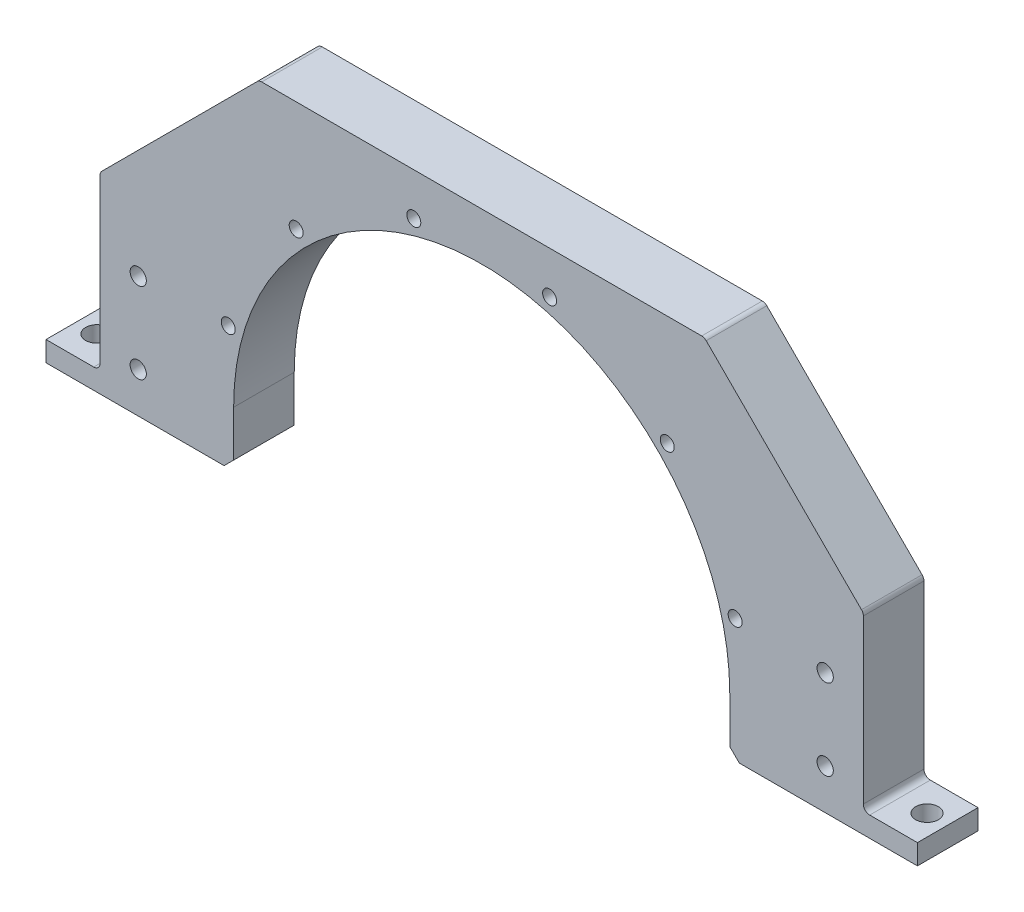
SolidWorks part; units mm, degrees
material "6061-T6 (SS)"
ref_plane "Front Plane" through (0, 0, 0) normal (0, 0, 1) x (1, 0, 0)
ref_plane "Top Plane" through (0, 0, 0) normal (0, 1, 0) x (1, 0, 0)
ref_plane "Right Plane" through (0, 0, 0) normal (1, 0, 0) x (0, 0, -1)
sketch "Sketch1" plane through (0, 0, 0) normal (0, 0, 1) x (1, 0, 0)
  line L1 (78, 0) -> (78, -17.4)
  line L2 (78, -17.4) -> (137, -17.4)
  line L3 (137, -17.4) -> (137, -11.05)
  line L4 (137, -11.05) -> (120, -11.05)
  line L5 (120, -11.05) -> (120, 93)
  line L6 (120, 93) -> (0, 93)
  line L11 (0, 93) -> (0, 78)
  arc A0 (0, 78) -> (78, 0) centre (0, 0) cw
  dimension "D1" = 78
  dimension "D2" = 120
  dimension "D3" = 6.35
  dimension "D4" = 17
  dimension "D5" = 15
  dimension "D6" = 17.4
extrude "Boss-Extrude1" add sketch "Sketch1" along normal blind 19.05
hole_wizard "Tapped Hole for #8-32 Helicoil1" positions "Sketch3" profile "Sketch2" tap size "#8-32" standard "Helicoil® Inch" end condition through all
sketch "Sketch3" plane through (0, 0, 19.05) normal (0, 0, 1) x (1, 0, 0)
  line L0 (0, 0) -> (21.3526, 79.6889)
  line L2 (0, 0) -> (58.3363, 58.3363)
  line L4 (0, 0) -> (79.6889, 21.3526)
  line L6 (21.3526, 79.6889) -> (39.8444, 69.0126)
  line L7 (39.8444, 69.0126) -> (58.3363, 58.3363)
  line L9 (58.3363, 58.3363) -> (69.0126, 39.8444)
  line L10 (69.0126, 39.8444) -> (79.6889, 21.3526)
  line L12 (21.3526, 79.6889) -> (0, 79.6889)
  line L13 (0, 93) -> (0, 78) construction
  line L15 (78, 0) -> (120, 0)
  line L16 (120, -11.05) -> (120, 93) construction
  line L18 (79.6889, 21.3526) -> (79.6889, 0)
  point P0 (21.3526, 79.6889)
  point P2 (58.3363, 58.3363)
  point P4 (79.6889, 21.3526)
  dimension "D1" = 82.5
sketch "Sketch2" plane through (21.3526, 79.6889, 19.05) normal (1, 0, 0) x (0, -1, 0)
  line L0 (0, 0) -> (0, 19.05)
  line L1 (0, 19.05) -> (2.1971, 19.05)
  line L2 (2.1971, 19.05) -> (2.1971, 0)
  line L5 (2.1971, 0) -> (0, 0)
  line L11 (0, -6.35) -> (0, 107.95) construction
  dimension "Thru Tap Drill Dia." = 4.3942
  dimension "Thru Tap Drill Depth" = 19.05
cosmetic thread "Hole Thread1" parameters "D1"=12.7, "D2"=5.2756
cosmetic thread "Hole Thread2" parameters "D1"=12.7, "D2"=5.2756
cosmetic thread "Hole Thread3" parameters "D1"=12.7, "D2"=5.2756
hole_wizard "1/4-20 Tapped Hole1" positions "Sketch7" profile "Sketch8" tap size "1/4-20" standard "ANSI Inch" end condition through all
sketch "Sketch7" plane through (0, 0, 19.05) normal (0, 0, 1) x (1, 0, 0)
  line L0 (108, 20.7) -> (108, -4.7)
  line L2 (78, -17.4) -> (137, -17.4) construction
  point P0 (108, 20.7)
  point P2 (108, -4.7)
  dimension "D1" = 108
  dimension "D2" = 25.4
  dimension "D3" = 12.7
sketch "Sketch8" plane through (108, 20.7, 19.05) normal (1, 0, 0) x (0, -1, 0)
  line L0 (0, 0) -> (0, 19.05)
  line L1 (0, 19.05) -> (2.5527, 19.05)
  line L2 (2.5527, 19.05) -> (2.5527, 0)
  line L5 (2.5527, 0) -> (0, 0)
  line L11 (0, -6.35) -> (0, 107.95) construction
  dimension "Thru Tap Drill Dia." = 5.1054
  dimension "Thru Tap Drill Depth" = 19.05
cosmetic thread "Hole Thread4" parameters "D2"=6.35
cosmetic thread "Hole Thread5" parameters "D2"=6.35
hole_wizard "1/4 Clearance Hole1" positions "Sketch5" profile "Sketch4" hole size "1/4" standard "ANSI Inch"
sketch "Sketch5" plane through (0, -11.05, 0) normal (0, 1, 0) x (1, 0, 0)
  line L2 (130.5, -9.525) -> (137, -9.525)
  line L3 (137, -19.05) -> (137, 0) construction
  point P0 (130.5, -9.525)
  dimension "D1" = 6.5
sketch "Sketch4" plane through (130.5, -11.05, 9.525) normal (1, 0, 0) x (0, 0, 1)
  line L0 (0, 0) -> (0, 14.8458)
  line L1 (0, 14.8458) -> (3.5712, 12.7)
  line L2 (3.5712, 12.7) -> (3.5712, 0)
  line L5 (3.5712, 0) -> (0, 0)
  line L10 (0, 14.8458) -> (-3.5712, 12.7) construction
  line L11 (0, -6.35) -> (0, 107.95) construction
  dimension "Hole Dia." = 7.1425
  dimension "Hole Depth" = 12.7
  dimension "Drill Angle" = 118
chamfer "Chamfer2" distance 3 angle 45 1 edges at (78, -17.4, 9.525)
chamfer "Chamfer3" distance 50 angle 45 1 edges at (120, 93, 9.525)
fillet "Fillet2" radius 2 3 edges at (120, -11.05, 9.525) (70, 93, 9.525) (120, 43, 9.525)
mirror "Mirror2" about plane through (0, 0, 0) normal (1, 0, 0) of bodies 105 103
